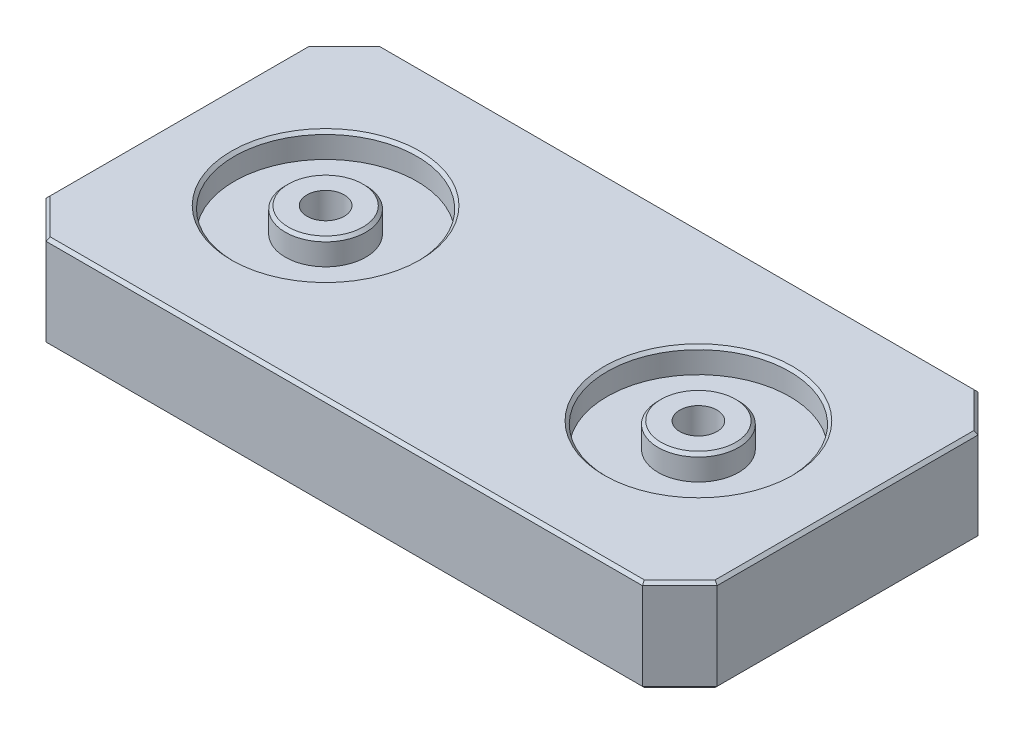
SolidWorks part; units mm, degrees
material "17-4 PH SSTL, H 1150"
ref_plane "Front" through (0, 0, 0) normal (0, 0, 1) x (1, 0, 0)
ref_plane "Top" through (0, 0, 0) normal (0, 1, 0) x (1, 0, 0)
ref_plane "Right" through (0, 0, 0) normal (1, 0, 0) x (0, 0, -1)
sketch "Sketch1" plane through (0, 0, 0) normal (0, 1, 0) x (1, 0, 0)
  line L1 (-57.15, 28.575) -> (57.15, 28.575)
  line L2 (-57.15, 28.575) -> (-57.15, -28.575)
  line L3 (-57.15, -28.575) -> (57.15, -28.575)
  line L4 (57.15, 28.575) -> (57.15, -28.575)
  point P4 (0, 28.575)
  point P5 (57.15, 0)
  dimension "D1" = 57.15
  dimension "D5" = 114.3
extrude "Extrude1" add sketch "Sketch1" along normal blind 15.875
sketch "Sketch3" plane through (0, 15.875, 0) normal (0, 1, 0) x (1, 0, 0)
  line L0 (-57.15, 22.225) -> (-50.8, 28.575)
  line L1 (-57.15, 28.575) -> (-57.15, -28.575) construction
  line L2 (-57.15, 28.575) -> (57.15, 28.575) construction
  line L3 (-50.8, 28.575) -> (-57.15, 28.575)
  line L4 (-57.15, 28.575) -> (-57.15, 22.225)
  line L5 (-57.15, -28.575) -> (-57.15, -22.225)
  line L6 (-57.15, -22.225) -> (-50.8, -28.575)
  line L7 (-57.15, -28.575) -> (57.15, -28.575) construction
  line L8 (-50.8, -28.575) -> (-57.15, -28.575)
  line L9 (57.15, -28.575) -> (57.15, -22.225)
  line L10 (57.15, 28.575) -> (57.15, -28.575) construction
  line L11 (57.15, -22.225) -> (50.8, -28.575)
  line L12 (50.8, -28.575) -> (57.15, -28.575)
  line L13 (57.15, 28.575) -> (57.15, 22.225)
  line L14 (57.15, 22.225) -> (50.8, 28.575)
  line L15 (50.8, 28.575) -> (57.15, 28.575)
  dimension "D1" = 6.35
extrude "Cut-Extrude1" cut sketch "Sketch3" against normal through all
sketch "Sketch4" plane through (0, 15.875, 0) normal (0, 1, 0) x (1, 0, 0)
  line L0 (-31.75, 0) -> (31.75, 0) construction
  circle A0 centre (-31.75, 0) radius 15.5575
  circle A1 centre (31.75, 0) radius 15.5575
  dimension "D3" = 31.115
  dimension "D2" = 63.5
extrude "Extrude7" cut sketch "Sketch4" against normal blind 4.191
sketch "Sketch6" plane through (0, 11.684, 0) normal (0, 1, 0) x (1, 0, 0)
  circle A0 centre (-31.75, 0) radius 6.858
  circle A1 centre (31.75, 0) radius 6.858
  circle A2 centre (-31.75, 0) radius 15.5575 construction
  circle A3 centre (31.75, 0) radius 15.5575 construction
  dimension "D1" = 13.716
extrude "Extrude8" add sketch "Sketch6" along normal up to surface (4.191 mm away) up to face at (31.75, 15.875, 15.5575)
chamfer "Chamfer1" distance 0.508 angle 45 20 edges at (-53.975, 0, -25.4) (-57.15, 0, 0) (-53.975, 0, 25.4) (0, 0, 28.575) (53.975, 0, 25.4) (57.15, 0, 0) (53.975, 0, -25.4) (0, 0, -28.575) (57.15, 15.875, 0) (53.975, 15.875, 25.4) (0, 15.875, 28.575) (-53.975, 15.875, 25.4) (-57.15, 15.875, 0) (-53.975, 15.875, -25.4) (0, 15.875, -28.575) (53.975, 15.875, -25.4) (-31.75, 15.875, 15.5575) (31.75, 15.875, 15.5575) (31.75, 15.875, 6.858) (-31.75, 15.875, 6.858)
sketch "Sketch7" plane through (0, 0, 0) normal (0, -1, 0) x (1, 0, 0)
  line L0 (-31.75, 15.875) -> (31.75, 15.875) construction
  line L1 (-31.75, 15.875) -> (-31.75, -15.875) construction
  line L2 (-31.75, -15.875) -> (31.75, -15.875) construction
  line L3 (31.75, 15.875) -> (31.75, -15.875) construction
  line L4 (0, 0) -> (-31.75, 0) construction
  line L5 (0, 0) -> (0, 15.875) construction
  circle A0 centre (-31.75, 15.875) radius 7.112
  circle A1 centre (-31.75, -15.875) radius 7.112
  circle A2 centre (31.75, 15.875) radius 7.112
  circle A3 centre (31.75, -15.875) radius 7.112
  dimension "D1" = 14.224
  dimension "D2" = 63.5
  dimension "D3" = 31.75
extrude "Cut-Extrude2" cut sketch "Sketch7" against normal blind 1.905
hole_wizard "1/4-20 Tapped Hole1" positions "Sketch11" profile "Sketch10" tap size "1/4-20" standard "Ansi Inch" end condition through all
sketch "Sketch11" plane through (0, 15.875, 0) normal (0, 1, 0) x (-1, 0, 0)
  point P0 (31.75, 0)
  point P1 (-31.75, 0)
sketch "Sketch10" plane through (-31.75, 15.875, 0) normal (1, 0, 0) x (0, 0, 1)
  line L0 (0, 0) -> (0, 15.875)
  line L1 (0, 15.875) -> (3.175, 15.875)
  line L2 (3.175, 15.875) -> (3.175, 0)
  line L5 (3.175, 0) -> (0, 0)
  line L11 (0, -6.35) -> (0, 107.95) construction
  dimension "Thread Major Dia." = 6.35
  dimension "Thru Tap Drill Depth" = 15.875
